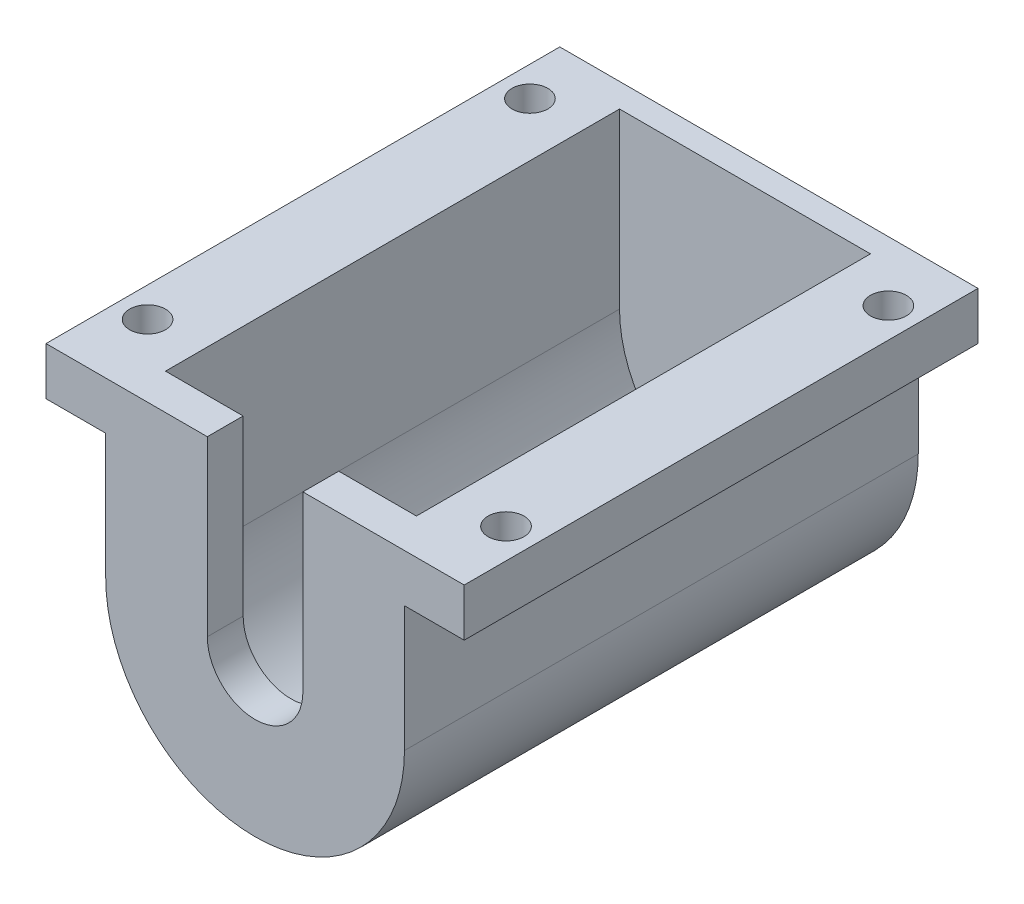
SolidWorks part; units mm, degrees
ref_plane "Alzado" through (0, 0, 0) normal (0, 0, 1) x (1, 0, 0)
ref_plane "Planta" through (0, 0, 0) normal (0, 1, 0) x (1, 0, 0)
ref_plane "Vista lateral" through (0, 0, 0) normal (1, 0, 0) x (0, 0, -1)
sketch "Croquis1" plane through (0, 0, 0) normal (0, 0, 1) x (1, 0, 0)
  line L0 (-10.5, 0) -> (-10.5, 10.5)
  line L1 (10.5, 10.5) -> (12.5, 10.5)
  line L2 (-10.5, 10.5) -> (-12.5, 10.5)
  line L3 (10.5, 10.5) -> (10.5, 0)
  line L4 (12.5, 10.5) -> (12.5, 0)
  line L5 (-12.5, 0) -> (-12.5, 10.5)
  arc A0 (-10.5, 0) -> (10.5, 0) centre (0, 0) ccw
  arc A1 (-12.5, 0) -> (12.5, 0) centre (0, 0) ccw
  dimension "D1" = 21
  dimension "D2" = 2
extrude "Saliente-Extruir1" add sketch "Croquis1" along normal blind 38
sketch "Croquis2" plane through (0, 0, 38) normal (0, 0, 1) x (1, 0, 0)
  line L0 (-12.5, 10.5) -> (-4, 10.5)
  line L1 (-4, 10.5) -> (-4, 0)
  line L2 (4, 0) -> (4, 10.5)
  line L3 (4, 10.5) -> (12.5, 10.5)
  line L4 (-12.5, 10.5) -> (-12.5, 0)
  line L5 (12.5, 10.5) -> (12.5, 0)
  arc A0 (-4, 0) -> (4, 0) centre (0, 0) ccw
  arc A1 (-12.5, 0) -> (12.5, 0) centre (0, 0) ccw
  dimension "D1" = 8
extrude "Saliente-Extruir2" add sketch "Croquis2" along normal blind 3
sketch "Croquis3" plane through (0, 0, 0) normal (0, 0, -1) x (-1, 0, 0)
  line L0 (-12.5, 10.5) -> (12.5, 10.5)
  line L1 (12.5, 10.5) -> (12.5, 0)
  line L2 (-12.5, 10.5) -> (-12.5, 0)
  arc A0 (-12.5, 0) -> (12.5, 0) centre (0, 0) ccw
extrude "Saliente-Extruir3" add sketch "Croquis3" along normal blind 2
sketch "Croquis4" plane through (0, 10.5, 0) normal (0, 1, 0) x (1, 0, 0)
  line L0 (-17.5, 2) -> (17.5, 2)
  line L1 (17.5, -41) -> (4, -41)
  line L2 (-17.5, -41) -> (-17.5, 2)
  line L3 (17.5, 2) -> (17.5, -41)
  line L5 (-10.5, 0) -> (10.5, 0) construction
  line L7 (12.5, -41) -> (12.5, 2) construction
  line L8 (-12.5, -41) -> (-12.5, 2) construction
  line L9 (-10.5, -38) -> (-4, -38)
  line L10 (-4, -38) -> (-4, -41)
  line L11 (-10.5, 0) -> (-10.5, -38)
  line L12 (-10.5, 0) -> (10.5, 0)
  line L13 (10.5, 0) -> (10.5, -38)
  line L14 (10.5, -38) -> (4, -38)
  line L15 (4, -38) -> (4, -41)
  line L16 (-4, -41) -> (-17.5, -41)
  circle A0 centre (-15, -3) radius 1.5
  circle A1 centre (15, -3) radius 1.5
  circle A2 centre (15, -35) radius 1.5
  circle A3 centre (-15, -35) radius 1.5
  dimension "D5" = 3
  dimension "D1" = 2
  dimension "D3" = 5
  dimension "D4" = 5
  dimension "D6" = 2
  dimension "D7" = 2
extrude "Saliente-Extruir4" add sketch "Croquis4" along normal blind 4
